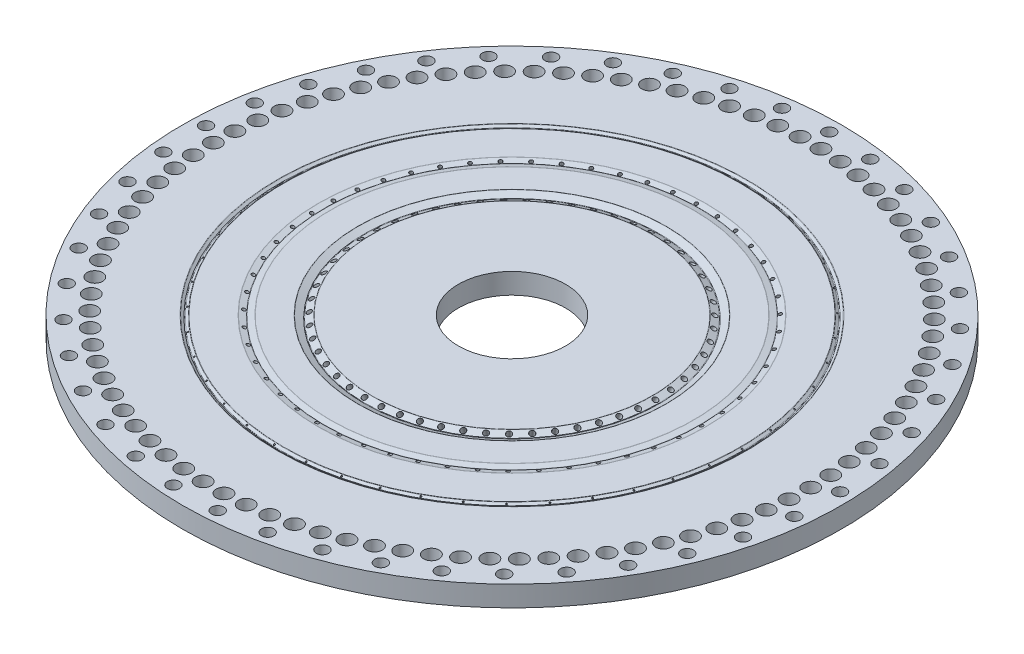
SolidWorks part; units mm, degrees
material "AISI 316 Stainless Steel Sheet (SS)"
ref_plane "Front Plane" through (0, 0, 0) normal (0, 0, 1) x (1, 0, 0)
ref_plane "Top Plane" through (0, 0, 0) normal (0, 1, 0) x (1, 0, 0)
ref_plane "Right Plane" through (0, 0, 0) normal (1, 0, 0) x (0, 0, -1)
sketch "FacePlateSketch" plane through (0, 0, 0) normal (0, 1, 0) x (1, 0, 0)
  circle A0 centre (0, 0) radius 101.6
  circle A1 centre (0, 0) radius 16.51
  dimension "D2" = 33.02
  dimension "D1" = 203.2
extrude "FacePlateOriginalBoss" add sketch "FacePlateSketch" along normal blind 6.35
sketch "Reference Diameters" plane through (0, 6.35, 0) normal (0, 1, 0) x (1, 0, 0)
  circle A0 centre (0, 0) radius 44.45 construction
  circle A1 centre (0, 0) radius 58.42 construction
  circle A2 centre (0, 0) radius 19.05 construction
  circle A3 centre (0, 0) radius 97.79 construction
  circle A4 centre (0, 0) radius 71.12 construction
  circle A5 centre (0, 0) radius 82.55 construction
  dimension "DGammaLOX" = 88.9
  dimension "D1" = 38.1
  dimension "D2" = 195.58
  dimension "D3" = 165.1
  dimension "Doublet Spacing" = 13.97
  dimension "D4" = 11.43
sketch "LOXDoubletSketch" plane through (0, 0, 0) normal (0, 0, 1) x (1, 0, 0)
  line L0 (0, 0) -> (44.45, 0) construction
  line L1 (45.3258, 6.35) -> (45.3258, -0.6709)
  line L2 (42.0519, -0.6709) -> (45.3258, -0.6709) construction
  line L3 (44.45, 0) -> (44.45, 6.35) construction
  line L4 (42.0519, -0.6709) -> (40.6131, 0) construction
  line L5 (45.3258, 6.35) -> (42.0519, -0.6709)
  line L6 (43.5742, 6.35) -> (40.3003, -0.6709)
  line L7 (45.3258, 6.35) -> (44.45, 6.35)
  line L8 (44.45, 6.35) -> (41.1761, -0.6709)
  line L9 (42.0519, -0.6709) -> (40.3003, -0.6709)
  line L10 (58.42, 6.35) -> (-58.42, 6.35) construction
  line L11 (44.45, 6.35) -> (43.5742, 6.35)
  line L12 (44.45, 6.35) -> (44.45, 12.7) construction
  line L13 (44.45, 6.35) -> (47.7239, 13.3709) construction
  dimension "D1" = 25
revolve "LOXDoubletCut" cut sketch "LOXDoubletSketch" angle 360 about L8
sketch "FUELDoubletSketch" plane through (0, 0, 0) normal (0, 0, 1) x (1, 0, 0)
  line L0 (0, 0) -> (58.42, 0) construction
  line L1 (57.8559, 6.35) -> (57.8559, -0.2735) construction
  line L2 (60.697, -0.2735) -> (57.8559, -0.2735) construction
  line L3 (58.42, 0) -> (58.42, 6.35) construction
  line L4 (59.5689, -0.2735) -> (60.6263, 0) construction
  line L5 (58.9841, 6.35) -> (60.697, -0.2735)
  line L6 (57.8559, 6.35) -> (59.5689, -0.2735)
  line L7 (58.9841, 6.35) -> (58.42, 6.35)
  line L8 (58.42, 6.35) -> (60.1329, -0.2735)
  line L9 (60.697, -0.2735) -> (59.5689, -0.2735)
  line L11 (58.42, 6.35) -> (57.8559, 6.35)
  line L15 (58.42, 0) -> (101.6, 0) construction
  dimension "D1" = 14.5
revolve "FUELDoubletCut" cut sketch "FUELDoubletSketch" angle 360 about L8
pattern_circular "DoubletToDoublets" count 55 over 360 about axis through (0, 6.35, 0) along (0, -1, 0) of "LOXDoubletCut", "FUELDoubletCut"
sketch "FilmCoolingOrificeSketch" plane through (0, 0, 0) normal (0, 0, 1) x (1, 0, 0)
  line L0 (0, 0) -> (71.12, 0) construction
  line L1 (71.3991, 6.35) -> (71.3991, -0.2622)
  line L2 (66.7691, -0.2622) -> (71.3991, -0.2622) construction
  line L3 (71.12, 0) -> (71.12, 6.35) construction
  line L4 (66.7691, -0.2622) -> (66.3946, 0) construction
  line L5 (71.3991, 6.35) -> (66.7691, -0.2622)
  line L6 (70.8409, 6.35) -> (66.211, -0.2622)
  line L7 (71.3991, 6.35) -> (71.12, 6.35)
  line L8 (71.12, 6.35) -> (66.4901, -0.2622)
  line L9 (66.7691, -0.2622) -> (66.211, -0.2622)
  line L11 (71.12, 6.35) -> (70.8409, 6.35)
  line L12 (71.12, 6.35) -> (71.12, 12.7) construction
  line L13 (71.12, 6.35) -> (75.7499, 12.9622) construction
  dimension "D1" = 35
revolve "OuterFilmCoolingOrifice" cut sketch "FilmCoolingOrificeSketch" angle 360 about L8
pattern_circular "OrificeToOrifices" count 47 over 360 about axis through (0, 6.35, 0) along (0, -1, 0) of "OuterFilmCoolingOrifice"
sketch "LOXPlenumSketch" plane through (0, 0, 0) normal (0, 0, 1) x (1, 0, 0)
  line L0 (0, 0) -> (21.59, 0) construction
  line L1 (0, 0) -> (44.45, 0) construction
  line L2 (21.59, 0) -> (21.59, 1.5875) construction
  line L3 (22.7016, 1.5875) -> (44.9259, 1.5875)
  line L4 (46.0375, 1.5875) -> (46.0375, 0) construction
  line L5 (58.42, 0) -> (101.6, 0) construction
  line L6 (19.05, 6.35) -> (19.05, 0) construction
  line L7 (19.05, 6.35) -> (-19.05, 6.35) construction
  line L8 (44.45, 6.35) -> (-44.45, 6.35) construction
  line L9 (21.59, 0) -> (46.0375, 0)
  line L10 (46.0375, 0) -> (44.9259, 1.5875)
  line L11 (21.59, 0) -> (22.7016, 1.5875)
  line L12 (21.59, 1.5875) -> (22.7016, 1.5875) construction
  line L13 (44.9259, 1.5875) -> (46.0375, 1.5875) construction
  line L14 (45.3258, 6.35) -> (43.5742, 6.35) construction
  line L15 (45.3258, 6.35) -> (43.5742, 6.35) construction
  line L16 (44.45, 6.35) -> (46.0375, 6.35) construction
  line L18 (46.0375, 6.35) -> (46.0375, 1.5875) construction
  dimension "D1" = 2.54
  dimension "D3" = 1.5875
  dimension "D4" = 35
  dimension "D5" = 35
revolve "LOXPlenum" cut sketch "LOXPlenumSketch" angle 360 about axis through (0, 6.35, 0) along (0, -1, 0)
sketch "FUELPlenumSketch" plane through (0, 0, 0) normal (0, 0, 1) x (1, 0, 0)
  line L0 (0, 0) -> (56.8325, 0) construction
  line L1 (-101.6, 0) -> (101.6, 0) construction
  line L2 (56.8325, 0) -> (56.8325, 1.5875) construction
  line L3 (57.9441, 1.5875) -> (70.6434, 1.5875)
  line L4 (71.755, 1.5875) -> (71.755, 0) construction
  line L5 (46.0375, 1.5875) -> (46.0375, 0) construction
  line L6 (46.0375, 1.5875) -> (46.0375, 0) construction
  line L7 (71.3991, 6.35) -> (70.8409, 6.35) construction
  line L8 (71.3991, 6.35) -> (70.8409, 6.35) construction
  line L9 (56.8325, 0) -> (71.755, 0)
  line L10 (71.755, 0) -> (70.6434, 1.5875)
  line L11 (56.8325, 0) -> (57.9441, 1.5875)
  line L12 (56.8325, 1.5875) -> (57.9441, 1.5875) construction
  line L13 (70.6434, 1.5875) -> (71.755, 1.5875) construction
  line L14 (71.12, 6.35) -> (71.755, 6.35) construction
  line L15 (58.9841, 6.35) -> (57.8559, 6.35) construction
  line L16 (58.9841, 6.35) -> (57.8559, 6.35) construction
  line L17 (58.42, 6.35) -> (56.8325, 6.35) construction
  line L18 (101.6, 6.35) -> (-101.6, 6.35) construction
  line L19 (56.8325, 6.35) -> (56.8325, 0) construction
  line L20 (71.755, 6.35) -> (71.755, 1.5875) construction
  dimension "D3" = 1.5875
  dimension "D4" = 35
  dimension "D5" = 35
revolve "FUELPlenum" cut sketch "FUELPlenumSketch" angle 360 about axis through (0, 6.35, 0) along (0, -1, 0)
sketch "MachinabilityDivotSketch" plane through (0, 0, 0) normal (0, 0, 1) x (1, 0, 0)
  line L0 (57.8559, 6.35) -> (59.5689, -0.2735) construction
  line L1 (45.3258, 6.35) -> (42.0519, -0.6709) construction
  line L2 (57.8559, 6.35) -> (59.4982, 0) construction
  line L3 (45.3258, 6.35) -> (43.105, 1.5875) construction
  line L5 (45.3258, 5.3494) -> (47.4716, 6.35)
  line L6 (58.42, 6.35) -> (-58.42, 6.35) construction
  line L7 (59.69, 6.35) -> (57.8559, 5.8757)
  line L8 (57.8559, 5.8757) -> (56.0219, 6.35)
  line L10 (56.0219, 6.35) -> (59.69, 6.35)
  line L11 (45.3258, 5.3494) -> (45.3258, 6.35) construction
  line L12 (57.8559, 5.8757) -> (57.8559, 6.35) construction
  line L13 (43.5742, 6.35) -> (41.3534, 1.5875) construction
  line L14 (41.3534, 1.5875) -> (43.105, 1.5875) construction
  line L15 (41.3534, 1.5875) -> (43.4992, 1.5875)
  line L16 (43.4992, 1.5875) -> (41.3534, 2.5881)
  line L17 (41.3534, 1.5875) -> (41.3534, 2.5881) construction
  line L18 (41.3534, 1.5875) -> (39.2076, 1.5875)
  line L19 (-44.9259, 1.5875) -> (44.9259, 1.5875) construction
  line L20 (39.2076, 1.5875) -> (41.3534, 2.5881)
  line L21 (59.4982, 0) -> (60.6263, 0) construction
  line L22 (59.4982, 0) -> (60.6263, 0) construction
  line L23 (43.1754, 1.5875) -> (43.1754, 1.7385) construction
  line L24 (41.3534, 1.5875) -> (43.105, 1.5875)
  line L25 (45.3258, 6.35) -> (43.5742, 6.35)
  line L26 (44.45, 6.35) -> (42.2292, 1.5875) construction
  line L27 (47.4716, 6.35) -> (43.18, 6.35)
  line L28 (43.18, 6.35) -> (45.3258, 5.3494)
  line L29 (58.9841, 6.35) -> (60.6263, 0) construction
  line L30 (57.8559, 6.35) -> (58.9841, 6.35) construction
  line L31 (58.42, 6.35) -> (59.6517, 1.5875) construction
  line L32 (59.0876, 1.5875) -> (60.2157, 1.5875) construction
  line L33 (58.3817, 1.5875) -> (60.2157, 1.5875)
  line L34 (58.3817, 1.5875) -> (60.2157, 2.0618)
  line L35 (60.2157, 2.0618) -> (60.2157, 1.5875) construction
  line L36 (72.3131, 6.35) -> (71.3991, 5.71)
  line L40 (-70.6434, 1.5875) -> (70.6434, 1.5875) construction
  line L41 (101.6, 6.35) -> (-101.6, 6.35) construction
  line L42 (71.3991, 5.71) -> (70.485, 6.35)
  line L43 (70.485, 6.35) -> (72.3131, 6.35)
  line L44 (71.3991, 5.71) -> (71.3991, 6.35) construction
  line L45 (71.3991, 6.35) -> (71.3991, -0.2622) construction
  line L46 (71.3991, 6.35) -> (66.7691, -0.2622) construction
  line L47 (68.4203, 1.5875) -> (67.7429, 2.0618)
  line L48 (67.7429, 2.0618) -> (60.2157, 2.0618)
  line L49 (67.7429, 2.0618) -> (67.7429, 1.5875) construction
  line L50 (67.7429, 1.5875) -> (68.4203, 1.5875)
  line L51 (70.8409, 6.35) -> (66.211, -0.2622) construction
  line L52 (70.8409, 6.35) -> (66.211, -0.2622) construction
  line L53 (71.12, 6.35) -> (66.4901, -0.2622) construction
  line L54 (71.12, 6.35) -> (66.4901, -0.2622) construction
  line L55 (67.5062, 1.5875) -> (68.0643, 1.5875) construction
  line L56 (67.5062, 1.5875) -> (68.0643, 1.5875) construction
  line L57 (67.7429, 1.5875) -> (60.2157, 1.5875)
  point P74 (67.7853, 1.5875)
  dimension "D3" = 1.27
  dimension "D4" = 1.27
  dimension "D6" = 0.635
revolve "MachinabilityDivot" cut sketch "MachinabilityDivotSketch" angle 360 about axis through (0, 6.35, 0) along (0, -1, 0)
fillet "MachinabilityFillets" radius 0.254 20 edges at (0, 6.35, 59.69) (0, 5.8757, 57.8559) (0, 6.35, 56.0219) (0, 6.35, 47.4716) (0, 5.3494, 45.3258) (0, 6.35, 43.18) (0, 1.5875, 44.9259) (0, 1.5875, 43.4992) (0, 2.5881, 41.3534) (0, 1.5875, 39.2076) (0, 1.5875, 22.7016) (0, 1.5875, 70.6434) (0, 1.5875, 58.3817) (0, 1.5875, 57.9441) (0, 1.5875, 68.4203) (0, 2.0618, 67.7429) (0, 2.0618, 60.2157) (0, 6.35, 72.3131) (0, 5.71, 71.3991) (0, 6.35, 70.485)
sketch "Sketch1" plane through (0, 0, 0) normal (0, 0, 1) x (1, 0, 0)
  line L0 (18.669, 0) -> (18.669, 1.3208)
  line L1 (-56.8325, 0) -> (56.8325, 0) construction
  line L2 (18.669, 1.3208) -> (20.9296, 1.3208)
  line L3 (20.9296, 1.3208) -> (20.9296, 0)
  line L4 (20.9296, 0) -> (18.669, 0)
  line L5 (53.4035, 0) -> (53.4035, 1.3208)
  line L6 (0, 0) -> (0, 7.6775) construction
  line L7 (53.4035, 1.3208) -> (56.0451, 1.3208)
  line L8 (56.0451, 1.3208) -> (56.0451, 0)
  line L9 (56.0451, 0) -> (53.4035, 0)
  line L14 (56.8325, 0) -> (57.9441, 1.5875) construction
  line L15 (46.0375, 0) -> (44.9259, 1.5875) construction
  line L16 (56.8325, 0) -> (57.9441, 1.5875) construction
  line L17 (46.0375, 0) -> (44.9259, 1.5875) construction
  line L18 (56.8325, 0) -> (46.0375, 0) construction
  point P10 (54.7243, 0)
  point P28 (19.7993, 0)
  dimension "D1" = 39.5986
  dimension "D2" = 2.2606
  dimension "D3" = 109.4486
  dimension "D4" = 1.3208
  dimension "D5" = 2.6416
  dimension "D6" = 1.3208
revolve "Oring and relife grove" cut sketch "Sketch1" angle 360 about L6
hole_wizard "#6 Clearance Hole1" positions "Sketch14" profile "Sketch3" hole size "#6" standard "ANSI Inch"
sketch "Sketch14" plane through (0, 6.35, 0) normal (0, 1, 0) x (1, 0, 0)
  circle A0 centre (0, 0) radius 97.79 construction
  point P0 (0, 97.79)
  point P17 (13.6097, 96.8383)
  point P18 (26.9546, 94.0018)
  point P19 (39.7748, 89.3356)
  point P20 (51.8208, 82.9306)
  point P21 (62.8582, 74.9115)
  point P22 (72.6721, 65.4343)
  point P23 (81.0716, 54.6835)
  point P24 (87.8931, 42.8683)
  point P25 (93.0038, 30.2188)
  point P26 (96.3044, 16.9811)
  point P27 (97.7304, 3.4128)
  point P28 (97.2543, -10.2218)
  point P29 (94.8852, -23.6575)
  point P30 (90.6693, -36.6328)
  point P31 (84.6886, -48.895)
  point P32 (77.0596, -60.2055)
  point P33 (67.9306, -70.3442)
  point P34 (57.4795, -79.1138)
  point P35 (45.9096, -86.3434)
  point P36 (33.4461, -91.8925)
  point P37 (20.3317, -95.6531)
  point P38 (6.8215, -97.5518)
  point P39 (-6.8215, -97.5518)
  point P40 (-20.3317, -95.6531)
  point P41 (-33.4461, -91.8925)
  point P42 (-45.9096, -86.3434)
  point P43 (-57.4795, -79.1138)
  point P44 (-67.9306, -70.3442)
  point P45 (-77.0596, -60.2055)
  point P46 (-84.6886, -48.895)
  point P47 (-90.6693, -36.6328)
  point P48 (-94.8852, -23.6575)
  point P49 (-97.2543, -10.2218)
  point P50 (-97.7304, 3.4128)
  point P51 (-96.3044, 16.9811)
  point P52 (-93.0038, 30.2188)
  point P53 (-87.8931, 42.8683)
  point P54 (-81.0716, 54.6835)
  point P55 (-72.6721, 65.4343)
  point P56 (-62.8582, 74.9115)
  point P57 (-51.8208, 82.9306)
  point P58 (-39.7748, 89.3356)
  point P59 (-26.9546, 94.0018)
  point P60 (-13.6097, 96.8383)
  dimension "D1" = 195.58
  dimension "D2" = 45
sketch "Sketch3" plane through (0, 6.35, -97.79) normal (1, 0, 0) x (0, 0, 1)
  line L0 (0, 0) -> (0, 6.35)
  line L1 (0, 6.35) -> (1.8986, 6.35)
  line L2 (1.8986, 6.35) -> (1.8986, 0)
  line L5 (1.8986, 0) -> (0, 0)
  line L11 (0, -6.35) -> (0, 107.95) construction
  dimension "Thru Hole Dia." = 3.7973
  dimension "Thru Hole Depth" = 6.35
hole_wizard "3/16 (0.1875) Dowel Hole1" positions "Sketch15" profile "Sketch6" hole size "3/16" standard "ANSI Inch"
sketch "Sketch15" plane through (0, 6.35, 0) normal (0, 1, 0) x (1, 0, 0)
  line L0 (0, 0) -> (0, 107.1775) construction
  line L2 (0, 0) -> (3.2134, 92.0189) construction
  circle A0 centre (0, 0) radius 92.075 construction
  point P0 (3.2134, 92.0189)
  point P17 (9.6245, 91.5706)
  point P18 (15.9887, 90.6762)
  point P19 (22.275, 89.34)
  point P20 (28.4527, 87.5685)
  point P21 (34.4919, 85.3705)
  point P22 (40.363, 82.7565)
  point P23 (46.0375, 79.7393)
  point P24 (51.4877, 76.3336)
  point P25 (56.687, 72.5561)
  point P26 (61.6102, 68.4251)
  point P27 (66.2332, 63.9607)
  point P28 (70.5335, 59.1847)
  point P29 (74.4902, 54.1203)
  point P30 (78.084, 48.7923)
  point P31 (81.2974, 43.2266)
  point P32 (84.1147, 37.4503)
  point P33 (86.5222, 31.4915)
  point P34 (88.5082, 25.3793)
  point P35 (90.0629, 19.1435)
  point P36 (91.1789, 12.8144)
  point P37 (91.8507, 6.4228)
  point P38 (92.075, 0)
  point P39 (91.8507, -6.4228)
  point P40 (91.1789, -12.8144)
  point P41 (90.0629, -19.1435)
  point P42 (88.5082, -25.3793)
  point P43 (86.5222, -31.4915)
  point P44 (84.1147, -37.4503)
  point P45 (81.2974, -43.2266)
  point P46 (78.084, -48.7923)
  point P47 (74.4902, -54.1203)
  point P48 (70.5335, -59.1847)
  point P49 (66.2332, -63.9607)
  point P50 (61.6102, -68.4251)
  point P51 (56.687, -72.5561)
  point P52 (51.4877, -76.3336)
  point P53 (46.0375, -79.7393)
  point P54 (40.363, -82.7565)
  point P55 (34.4919, -85.3705)
  point P56 (28.4527, -87.5685)
  point P57 (22.275, -89.34)
  point P58 (15.9887, -90.6762)
  point P59 (9.6245, -91.5706)
  point P60 (3.2134, -92.0189)
  point P61 (-3.2134, -92.0189)
  point P62 (-9.6245, -91.5706)
  point P63 (-15.9887, -90.6762)
  point P64 (-22.275, -89.34)
  point P65 (-28.4527, -87.5685)
  point P84 (-34.4919, -85.3705)
  point P85 (-40.363, -82.7565)
  point P86 (-46.0375, -79.7393)
  point P87 (-51.4877, -76.3336)
  point P88 (-56.687, -72.5561)
  point P89 (-61.6102, -68.4251)
  point P90 (-66.2332, -63.9607)
  point P91 (-70.5335, -59.1847)
  point P92 (-74.4902, -54.1203)
  point P93 (-78.084, -48.7923)
  point P94 (-81.2974, -43.2266)
  point P95 (-84.1147, -37.4503)
  point P96 (-86.5222, -31.4915)
  point P97 (-88.5082, -25.3793)
  point P98 (-90.0629, -19.1435)
  point P99 (-91.1789, -12.8144)
  point P100 (-91.8507, -6.4228)
  point P101 (-92.075, 0)
  point P102 (-91.8507, 6.4228)
  point P103 (-91.1789, 12.8144)
  point P104 (-90.0629, 19.1435)
  point P105 (-88.5082, 25.3793)
  point P106 (-86.5222, 31.4915)
  point P107 (-84.1147, 37.4503)
  point P108 (-81.2974, 43.2266)
  point P109 (-78.084, 48.7923)
  point P110 (-74.4902, 54.1203)
  point P111 (-70.5335, 59.1847)
  point P112 (-66.2332, 63.9607)
  point P113 (-61.6102, 68.4251)
  point P114 (-56.687, 72.5561)
  point P115 (-51.4877, 76.3336)
  point P116 (-46.0375, 79.7393)
  point P117 (-40.363, 82.7565)
  point P118 (-34.4919, 85.3705)
  point P119 (-28.4527, 87.5685)
  point P120 (-22.275, 89.34)
  point P121 (-15.9887, 90.6762)
  point P122 (-9.6245, 91.5706)
  point P123 (-3.2134, 92.0189)
  dimension "D1" = 184.15
  dimension "D3" = 2
  dimension "D2" = 90
sketch "Sketch6" plane through (3.2134, 6.35, -92.0189) normal (1, 0, 0) x (0, 0, 1)
  line L0 (0, 0) -> (0, 6.35)
  line L1 (0, 6.35) -> (2.3812, 6.35)
  line L2 (2.3812, 6.35) -> (2.3812, 0)
  line L5 (2.3812, 0) -> (0, 0)
  line L11 (0, -6.35) -> (0, 107.95) construction
  dimension "Thru Hole Dia." = 4.7625
  dimension "Thru Hole Depth" = 6.35
equation "\"RGammaLOX\"=1.75"
equation "\"Spacing\"=0.55"
equation "\"FacePlateDiameter\"= 8"
equation "\"GammaLOX\"= 25"
equation "\"LOXDoubletDiameter\"= 0.0625"
equation "\"FacePlateThickness\"= 0.25"
equation "\"NumberofHoles\"= 55"
equation "\"GammaFUEL\"= 14.5"
equation "\"FUELDoubletDiameter\"= 0.043"
equation "\"D2@FUELDoubletSketch\"=\"FUELDoubletDiameter\""
equation "\"D1@FUELDoubletSketch\"=\"GammaFUEL\""
equation "\"D2@LOXDoubletSketch\"=\"LOXDoubletDiameter\""
equation "\"D1@LOXDoubletSketch\"=\"GammaLOX\""
equation "\"Doublet Spacing@Reference Diameters\"=\"Spacing\""
equation "\"DGammaLOX@Reference Diameters\"=\"RGammaLOX\"*2"
equation "\"D1@FacePlateOriginalBoss\"=\"FacePlateThickness\""
equation "\"D1@DoubletToDoublets\"=\"NumberofHoles\""
equation "\"RPlugInitial\"= 0.75"
equation "\"D1@Reference Diameters\"=\"RPlugInitial\"*2"
equation "\"LOXPlenumSpacing\"= 0.5"
equation "\"LOXPlenumThickness\"= 0.0625"
equation "\"D3@LOXPlenumSketch\"=\"LOXPlenumThickness\""
equation "\"MachinabilityTolerance\"= 0.05"
equation "\"D1@MachinabilityDivotSketch\"=\"MachinabilityTolerance\""
equation "\"D2@MachinabilityDivotSketch\"=\"MachinabilityTolerance\""
equation "\"D3@MachinabilityDivotSketch\"=\"MachinabilityTolerance\""
equation "\"MachinableFillets\"= 0.015"
equation "\"FUELPlenumSpacing\"= 0.75"
equation "\"FUELPlenumThickness\"= 0.0625"
equation "\"D3@FUELPlenumSketch\"=\"FUELPlenumThickness\""
equation "\"OringGroove\"= 0.3"
equation "\"D4@MachinabilityDivotSketch\"=\"MachinabilityTolerance\""
equation "\"FilmCoolingSpacing\"= 0.45"
equation "\"BoltSpacing\"= 7.7"
equation "\"D2@Reference Diameters\"=\"BoltSpacing\""
equation "\"NumberBoltHoles\"= 45"
equation "\"InnerChamberDiameter\"= 6.5"
equation "\"D3@Reference Diameters\"=\"InnerChamberDiameter\""
equation "\"D4@Reference Diameters\"=\"FilmCoolingSpacing\""
equation "\"OuterFilmCoolingOrificeDiameter\"= 0.018"
equation "\"D2@FilmCoolingOrificeSketch\"=\"OuterFilmCoolingOrificeDiameter\""
equation "\"NumberFilmCoolingHoles\"= 47"
equation "\"D1@OrificeToOrifices\"=\"NumberFilmCoolingHoles\""
equation "\"D5@MachinabilityDivotSketch\"=\"MachinabilityTolerance\"/2"
equation "\"D6@MachinabilityDivotSketch\"=\"MachinabilityTolerance\"/2"
equation "\"GammaOuterFilmCooling\"= 35"
equation "\"D1@FilmCoolingOrificeSketch\"=\"GammaOuterFilmCooling\""
equation "\"D1@FUELPlenumSketch\"=\"MachinabilityTolerance\"*1.25"
equation "\"D2@FUELPlenumSketch\"=\"MachinabilityTolerance\"/2"
equation "\"D2@LOXPlenumSketch\"=\"MachinabilityTolerance\"*1.25"
equation "\"D1@Sketch14\" = \"BoltSpacing\""
equation "\"numberOfOuterFuelHoles\"= 90"
equation "\"DiameterOfOuterFuelHoles\"= 7.25"
equation "\"D1@Sketch12\" = \"DiameterOfOuterFuelHoles\""
equation "\"D2@Sketch12\" = \"numberOfOuterFuelHoles\""
equation "\"D1@FacePlateSketch\"=\"FacePlateDiameter\""
equation "\"D2@Sketch14\" = \"NumberBoltHoles\""
equation "\"D3@Sketch12\"=360/\"numberOfOuterFuelHoles\"/2"
